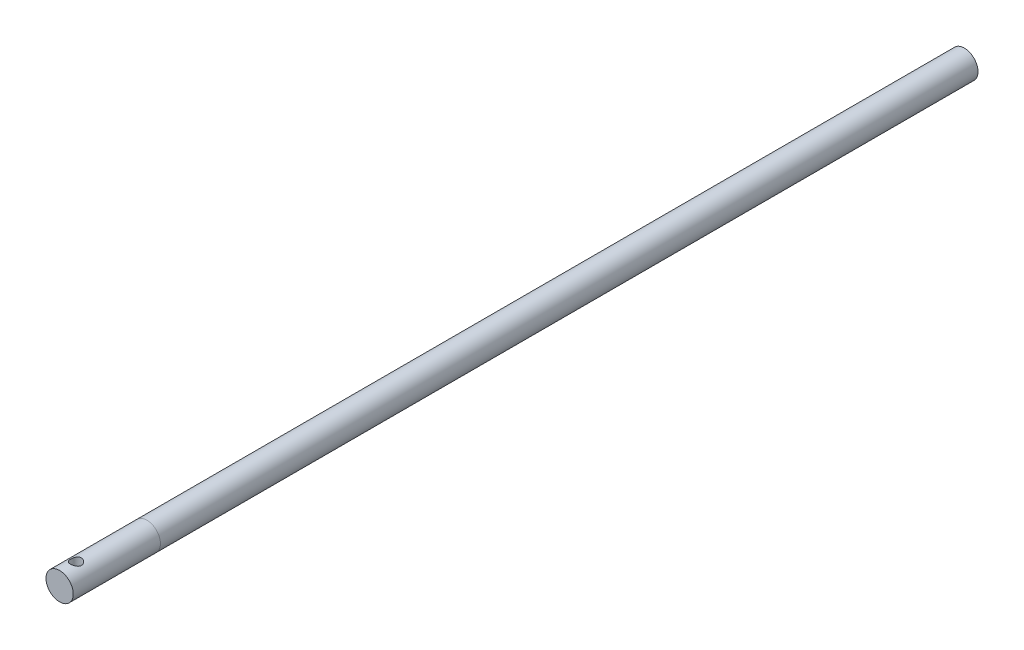
SolidWorks part; units mm, degrees
ref_plane "前视基准面" through (0, 0, 0) normal (0, 0, 1) x (1, 0, 0)
ref_plane "上视基准面" through (0, 0, 0) normal (0, 1, 0) x (1, 0, 0)
ref_plane "右视基准面" through (0, 0, 0) normal (1, 0, 0) x (0, 0, -1)
sketch "草图1" plane through (0, 0, 0) normal (0, 0, 1) x (1, 0, 0)
  circle A0 centre (0, 0) radius 2.5
  dimension "D1" = 5
extrude "凸台-拉伸1" add sketch "草图1" along normal blind 150
sketch "草图2" plane through (0, 0, 150) normal (0, 0, 1) x (1, 0, 0)
  circle A0 centre (0, 0) radius 2.5
  dimension "D1" = 5
extrude "凸台-拉伸2" add sketch "草图2" along normal blind 16 separate body
cosmetic thread "装饰螺纹线1" parameters "D2"=4
sketch "草图3" plane through (0, 0, 0) normal (0, 1, 0) x (1, 0, 0)
  line L0 (-2.5, -166) -> (2.5, -166) construction
  circle A0 centre (0, -163) radius 1
  dimension "D1" = 2
  dimension "D2" = 3
extrude "切除-拉伸1" cut sketch "草图3" against normal through all both and the other way through all
